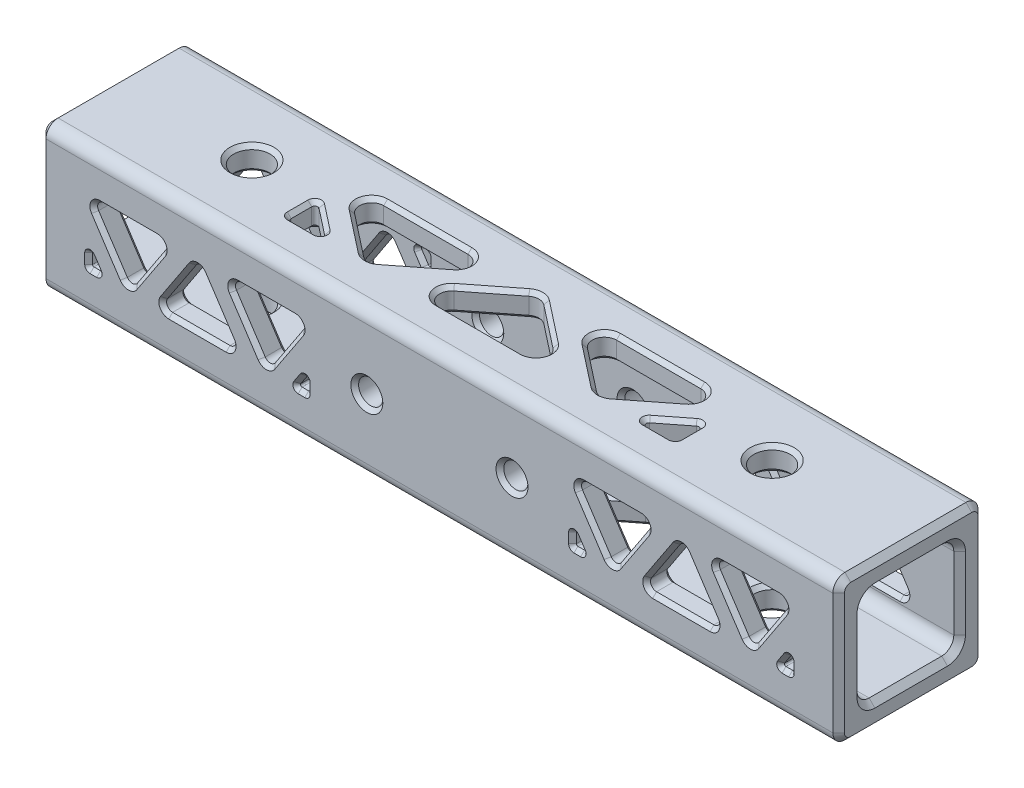
SolidWorks part; units mm, degrees
ref_plane "Front Plane" through (0, 0, 0) normal (0, 0, 1) x (1, 0, 0)
ref_plane "Top Plane" through (0, 0, 0) normal (0, 1, 0) x (1, 0, 0)
ref_plane "Right Plane" through (0, 0, 0) normal (1, 0, 0) x (0, 0, -1)
sketch "Sketch1" plane through (0, 0, 0) normal (1, 0, 0) x (0, 0, -1)
  line L1 (-6.35, -6.35) -> (6.35, -6.35)
  line L2 (-6.35, -6.35) -> (-6.35, 6.35)
  line L3 (-6.35, 6.35) -> (6.35, 6.35)
  line L4 (6.35, -6.35) -> (6.35, 6.35)
  line L5 (-6.35, -6.35) -> (6.35, 6.35) construction
  line L6 (-6.35, 6.35) -> (6.35, -6.35) construction
  line L7 (-9.525, -9.525) -> (9.525, -9.525)
  line L8 (-9.525, -9.525) -> (-9.525, 9.525)
  line L9 (-9.525, 9.525) -> (9.525, 9.525)
  line L10 (9.525, -9.525) -> (9.525, 9.525)
  line L11 (-9.525, -9.525) -> (9.525, 9.525) construction
  line L12 (-9.525, 9.525) -> (9.525, -9.525) construction
  point P0 (0, 0)
  point P6 (0, 0)
  dimension "D1" = 19.05
  dimension "D2" = 12.7
extrude "Boss-Extrude1" add sketch "Sketch1" along normal mid plane 104.775 contours L9 L10 L7 L8
hole_wizard "3/16 (0.1875) Diameter Hole1" positions "Sketch2" profile "Sketch3" hole size "3/16" standard "ANSI Inch" end condition through all
sketch "Sketch2" plane through (0, 9.525, 0) normal (0, 1, 0) x (1, 0, 0)
  line L0 (34.1313, 0) -> (-34.1313, 0) construction
  line L1 (34.1313, 0) -> (52.3875, 0) construction
  line L2 (52.3875, 9.525) -> (52.3875, -9.525) construction
  point P0 (-34.1313, 0)
  point P2 (34.1313, 0)
  dimension "D1" = 18.2562
sketch "Sketch3" plane through (-34.1313, 9.525, 0) normal (1, 0, 0) x (0, 0, 1)
  line L0 (0, 0) -> (0, 19.05)
  line L1 (0, 19.05) -> (2.3812, 19.05)
  line L2 (2.3812, 19.05) -> (2.3812, 0)
  line L5 (2.3812, 0) -> (0, 0)
  line L11 (0, -6.35) -> (0, 107.95) construction
  dimension "Thru Hole Dia." = 4.7625
  dimension "Thru Hole Depth" = 19.05
hole_wizard "1/8 (0.125) Diameter Hole1" positions "Sketch6" profile "Sketch7" hole size "1/8" standard "ANSI Inch" end condition through all
sketch "Sketch6" plane through (0, 0, -9.525) normal (0, 0, -1) x (-1, 0, 0)
  line L2 (-9.525, 0) -> (9.525, 0) construction
  point P18 (9.525, 0)
  point P20 (-9.525, 0)
  dimension "D5" = 19.05
sketch "Sketch7" plane through (9.525, 0, -9.525) normal (1, 0, 0) x (0, 1, 0)
  line L0 (0, 0) -> (0, 19.05)
  line L1 (0, 19.05) -> (1.5875, 19.05)
  line L2 (1.5875, 19.05) -> (1.5875, 0)
  line L5 (1.5875, 0) -> (0, 0)
  line L11 (0, -6.35) -> (0, 107.95) construction
  dimension "Thru Hole Dia." = 3.175
  dimension "Thru Hole Depth" = 19.05
sketch "Sketch8" plane through (0, 9.525, 0) normal (0, 1, 0) x (1, 0, 0)
  line L0 (-34.1313, 0) -> (-34.1313, 9.525) construction
  line L1 (52.3875, 9.525) -> (-52.3875, 9.525) construction
  line L2 (-34.1313, 0) -> (-34.1313, -9.525) construction
  line L3 (52.3875, -9.525) -> (-52.3875, -9.525) construction
  line L4 (-31.75, 0) -> (-31.75, -9.525) construction
  line L5 (-31.75, 0) -> (-31.75, 9.525) construction
  line L6 (34.1313, 0) -> (34.1313, 9.525) construction
  line L7 (34.1313, 0) -> (34.1313, -9.525) construction
  line L8 (31.75, 0) -> (31.75, -9.525) construction
  line L9 (31.75, 0) -> (31.75, 9.525) construction
  line L10 (-25.4, 9.525) -> (-25.4, -9.525) construction
  line L11 (25.4, 9.525) -> (25.4, -9.525) construction
  line L12 (-31.75, 0) -> (-25.4, 0) construction
  line L13 (25.4, 0) -> (31.75, 0) construction
  line L14 (-25.4, 3.9688) -> (25.4, 3.9688) construction
  line L15 (25.4, -3.9688) -> (-25.4, -3.9688) construction
  line L16 (0, -3.9688) -> (0, -9.525) construction
  line L17 (0, 3.9688) -> (0, 9.525) construction
  line L18 (-25.4, -0.0653) -> (-25.4, -3.9688)
  line L19 (-25.4, -3.9688) -> (-20.42, -3.9688)
  line L20 (-20.42, -3.9688) -> (-25.4, -0.0653)
  line L21 (-25.4, 3.9688) -> (-15.2733, -3.9688)
  line L22 (-15.2733, -3.9688) -> (-5.1467, 3.9688)
  line L23 (-5.1467, 3.9688) -> (-25.4, 3.9688)
  line L24 (-10.1267, -3.9688) -> (0, 3.9688)
  line L25 (0, 3.9688) -> (10.1267, -3.9688)
  line L26 (10.1267, -3.9688) -> (-10.1267, -3.9688)
  line L27 (25.4, 3.9688) -> (15.2733, -3.9688)
  line L28 (15.2733, -3.9688) -> (5.1467, 3.9688)
  line L29 (5.1467, 3.9688) -> (25.4, 3.9688)
  line L30 (25.4, -3.9688) -> (25.4, -0.0653)
  line L31 (25.4, -0.0653) -> (20.42, -3.9688)
  line L32 (20.42, -3.9688) -> (25.4, -3.9688)
  line L33 (-22.91, -2.017) -> (-20.9514, 0.4818) construction
  line L34 (22.91, -2.017) -> (20.9514, 0.4818) construction
  line L35 (-5.0633, 0) -> (-7.022, 2.4989) construction
  line L36 (5.0633, 0) -> (7.022, 2.4989) construction
  circle A0 centre (-34.1313, 0) radius 2.3813 construction
  circle A1 centre (34.1313, 0) radius 2.3813 construction
  dimension "D1" = 7.9375
  dimension "D2" = 6.35
  dimension "D3" = 3.175
extrude "Cut-Extrude1" cut sketch "Sketch8" against normal up to next (3.175 mm away) contours L21 L22 L23
sketch "Sketch9" plane through (0, 0, 9.525) normal (0, 0, 1) x (1, 0, 0)
  line L0 (-9.525, 0) -> (-9.525, -9.525) construction
  line L1 (52.3875, -9.525) -> (-52.3875, -9.525) construction
  line L2 (-9.525, 0) -> (-9.525, 9.525) construction
  line L3 (52.3875, 9.525) -> (-52.3875, 9.525) construction
  line L4 (-11.1125, 0) -> (-11.1125, -9.525) construction
  line L5 (-11.1125, 0) -> (-11.1125, 9.525) construction
  line L6 (-46.0375, 3.9688) -> (-46.0375, -3.9687) construction
  line L7 (-46.0375, -3.9687) -> (-17.4625, -3.9688) construction
  line L8 (-11.1125, 0) -> (-17.4625, 0) construction
  line L9 (-46.0375, 0) -> (-52.3875, 0) construction
  line L10 (-52.3875, 9.525) -> (-52.3875, -9.525) construction
  line L11 (-46.0375, 3.9688) -> (-17.4625, 3.9688) construction
  line L12 (-17.4625, -3.9688) -> (-17.4625, 3.9688) construction
  line L13 (-31.75, -3.9687) -> (-31.75, -9.525) construction
  line L14 (-31.75, 3.9687) -> (-31.75, 9.525) construction
  line L15 (9.525, 0) -> (9.525, -9.525) construction
  line L16 (9.525, 0) -> (9.525, 9.525) construction
  line L17 (11.1125, 0) -> (11.1125, -9.525) construction
  line L18 (11.1125, 0) -> (11.1125, 9.525) construction
  line L19 (17.4625, 3.9688) -> (17.4625, -3.9688) construction
  line L20 (17.4625, -3.9688) -> (46.0375, -3.9688) construction
  line L21 (46.0375, -3.9688) -> (46.0375, 3.9688) construction
  line L22 (46.0375, 3.9688) -> (17.4625, 3.9688) construction
  line L23 (11.1125, 0) -> (17.4625, 0) construction
  line L24 (46.0375, 0) -> (52.3875, 0) construction
  line L25 (52.3875, 9.525) -> (52.3875, -9.525) construction
  line L26 (31.75, -3.9688) -> (31.75, -9.525) construction
  line L27 (31.75, 3.9688) -> (31.75, 9.525) construction
  line L28 (-7.9375, 0) -> (-7.9375, -9.525) construction
  line L29 (-7.9375, 0) -> (-7.9375, 9.525) construction
  line L30 (7.9375, 0) -> (7.9375, -9.525) construction
  line L31 (7.9375, 0) -> (7.9375, 9.525) construction
  line L32 (-1.5875, 3.9687) -> (1.5875, 3.9687) construction
  line L33 (1.5875, 3.9687) -> (1.5875, -3.9687) construction
  line L34 (1.5875, -3.9687) -> (-1.5875, -3.9687) construction
  line L35 (-1.5875, -3.9687) -> (-1.5875, 3.9687) construction
  line L36 (-7.9375, 0) -> (-1.5875, 0) construction
  line L37 (1.5875, 0) -> (7.9375, 0) construction
  line L38 (-46.0375, 3.9688) -> (-40.7961, -3.9688)
  line L39 (-40.7961, -3.9688) -> (-35.5548, 3.9688)
  line L40 (-35.5548, 3.9688) -> (-46.0375, 3.9688)
  line L41 (-36.9914, -3.9688) -> (-31.75, 3.9687)
  line L42 (-31.75, 3.9687) -> (-26.5086, -3.9688)
  line L43 (-26.5086, -3.9688) -> (-36.9914, -3.9688)
  line L44 (-17.4625, 3.9688) -> (-22.7039, -3.9688)
  line L45 (-22.7039, -3.9688) -> (-27.9452, 3.9688)
  line L46 (-27.9452, 3.9688) -> (-17.4625, 3.9688)
  line L47 (-22.7039, -3.9688) -> (-22.7039, 3.9688) construction
  line L48 (-31.75, 3.9687) -> (-31.75, -3.9687) construction
  line L49 (-40.7961, -3.9688) -> (-40.7961, 3.9688) construction
  line L50 (-46.0375, -1.7931) -> (-46.0375, -3.9687)
  line L51 (-46.0375, -3.9687) -> (-44.6009, -3.9688)
  line L52 (-44.6009, -3.9688) -> (-46.0375, -1.7931)
  line L53 (-17.4625, -3.9688) -> (-17.4625, -1.7931)
  line L54 (-17.4625, -1.7931) -> (-18.8991, -3.9688)
  line L55 (-18.8991, -3.9688) -> (-17.4625, -3.9688)
  line L56 (-18.1808, -2.8809) -> (-20.8303, -1.1314) construction
  line L57 (-45.3192, -2.8809) -> (-42.6697, -1.1314) construction
  line L58 (-34.3707, 0) -> (-37.0202, 1.7495) construction
  line L59 (-29.1293, 0) -> (-26.4798, 1.7495) construction
  line L60 (17.4625, 3.9688) -> (22.7039, -3.9688)
  line L61 (22.7039, -3.9688) -> (27.9452, 3.9688)
  line L62 (27.9452, 3.9688) -> (17.4625, 3.9688)
  line L63 (26.5086, -3.9688) -> (31.75, 3.9688)
  line L64 (31.75, 3.9688) -> (36.9914, -3.9688)
  line L65 (36.9914, -3.9688) -> (26.5086, -3.9688)
  line L66 (46.0375, 3.9688) -> (40.7961, -3.9688)
  line L67 (40.7961, -3.9688) -> (35.5548, 3.9688)
  line L68 (35.5548, 3.9688) -> (46.0375, 3.9688)
  line L69 (17.4625, -1.7931) -> (17.4625, -3.9688)
  line L70 (17.4625, -3.9688) -> (18.8991, -3.9688)
  line L71 (18.8991, -3.9688) -> (17.4625, -1.7931)
  line L72 (46.0375, -1.7931) -> (46.0375, -3.9688)
  line L73 (46.0375, -3.9688) -> (44.6009, -3.9688)
  line L74 (44.6009, -3.9688) -> (46.0375, -1.7931)
  line L75 (18.1808, -2.8809) -> (20.8303, -1.1314) construction
  line L76 (29.1293, 0) -> (26.4798, 1.7495) construction
  line L77 (34.3707, 0) -> (37.0202, 1.7495) construction
  line L78 (45.3192, -2.8809) -> (42.6697, -1.1314) construction
  circle A0 centre (-9.525, 0) radius 1.5875 construction
  circle A1 centre (9.525, 0) radius 1.5875 construction
  dimension "D1" = 6.35
  dimension "D2" = 7.9375
  dimension "D3" = 7.9375
  dimension "D4" = 6.35
  dimension "D5" = 3.175
extrude "Cut-Extrude2" cut sketch "Sketch9" against normal up to next (3.175 mm away)
ref_axis "Axis1" through (57.6262, 0, 0) along (-1, 0, 0)
pattern_circular "CirPattern1" count 2 over 360 about axis through (57.6262, 0, 0) along (-1, 0, 0) of "Cut-Extrude1"
pattern_circular "CirPattern2" count 2 over 360 about axis through (57.6262, 0, 0) along (-1, 0, 0) of "Cut-Extrude2"
fillet "Fillet1" radius 1.5875 26 edges at (0, -6.35, -6.35) (0, 6.35, -6.35) (0, 6.35, 6.35) (0, -6.35, 6.35) (0, -9.525, -9.525) (0, 9.525, -9.525) (0, -9.525, 9.525) (0, 9.525, 9.525) (25.4, -7.9375, 3.9688) (5.1467, -7.9375, 3.9688) (15.2733, -7.9375, -3.9687) (0, -7.9375, 3.9688) (10.1267, -7.9375, -3.9688) (-10.1267, -7.9375, -3.9688) (-5.1467, -7.9375, 3.9688) (-25.4, -7.9375, 3.9688) (-15.2733, -7.9375, -3.9688) (25.4, 7.9375, -3.9688) (5.1467, 7.9375, -3.9687) (15.2733, 7.9375, 3.9688) (10.1267, 7.9375, 3.9688) (0, 7.9375, -3.9688) (-10.1267, 7.9375, 3.9687) (-5.1467, 7.9375, -3.9688) (-25.4, 7.9375, -3.9687) (-15.2733, 7.9375, 3.9688)
fillet "Fillet4" radius 0.7937 36 edges at (46.0375, 3.9688, 7.9375) (40.7961, -3.9688, 7.9375) (35.5548, 3.9688, 7.9375) (31.75, 3.9688, 7.9375) (36.9914, -3.9688, 7.9375) (26.5086, -3.9688, 7.9375) (17.4625, 3.9688, 7.9375) (27.9452, 3.9688, 7.9375) (22.7039, -3.9688, 7.9375) (-17.4625, 3.9688, 7.9375) (-22.7039, -3.9688, 7.9375) (-27.9452, 3.9688, 7.9375) (-26.5086, -3.9688, 7.9375) (-36.9914, -3.9688, 7.9375) (-31.75, 3.9687, 7.9375) (-35.5548, 3.9688, 7.9375) (-40.7961, -3.9688, 7.9375) (-46.0375, 3.9688, 7.9375) (-40.7961, 3.9688, -7.9375) (-46.0375, -3.9688, -7.9375) (-35.5548, -3.9688, -7.9375) (-36.9914, 3.9688, -7.9375) (-26.5086, 3.9688, -7.9375) (-31.75, -3.9687, -7.9375) (-27.9452, -3.9688, -7.9375) (-17.4625, -3.9688, -7.9375) (-22.7039, 3.9688, -7.9375) (17.4625, -3.9688, -7.9375) (27.9452, -3.9688, -7.9375) (22.7039, 3.9688, -7.9375) (26.5086, 3.9687, -7.9375) (36.9914, 3.9688, -7.9375) (31.75, -3.9688, -7.9375) (35.5548, -3.9688, -7.9375) (40.7961, 3.9688, -7.9375) (46.0375, -3.9688, -7.9375)
fillet "Fillet2" radius 0.3969 12 edges at (20.42, 7.9375, 3.9688) (25.4, 7.9375, 0.0653) (25.4, 7.9375, 3.9688) (-25.4, 7.9375, 0.0653) (-20.42, 7.9375, 3.9688) (-25.4, 7.9375, 3.9688) (-25.4, -7.9375, -0.0653) (-20.42, -7.9375, -3.9688) (-25.4, -7.9375, -3.9688) (20.42, -7.9375, -3.9688) (25.4, -7.9375, -0.0653) (25.4, -7.9375, -3.9688)
fillet "Fillet3" radius 0.1984 24 edges at (-46.0375, 3.9687, -7.9375) (-46.0375, 1.7931, -7.9375) (-44.6009, 3.9688, -7.9375) (-18.8991, 3.9688, -7.9375) (-17.4625, 1.7931, -7.9375) (-17.4625, 3.9688, -7.9375) (17.4625, 3.9688, -7.9375) (17.4625, 1.7931, -7.9375) (18.8991, 3.9688, -7.9375) (44.6009, 3.9688, -7.9375) (46.0375, 3.9688, -7.9375) (46.0375, 1.7931, -7.9375) (46.0375, -3.9688, 7.9375) (46.0375, -1.7931, 7.9375) (44.6009, -3.9688, 7.9375) (18.8991, -3.9688, 7.9375) (17.4625, -1.7931, 7.9375) (17.4625, -3.9688, 7.9375) (-18.8991, -3.9688, 7.9375) (-17.4625, -1.7931, 7.9375) (-17.4625, -3.9688, 7.9375) (-44.6009, -3.9688, 7.9375) (-46.0375, -1.7931, 7.9375) (-46.0375, -3.9687, 7.9375)
chamfer "Chamfer1" distance 0.762 angle 45 32 edges at (-52.3875, 5.885, 5.885) (-52.3875, 6.35, 0) (-52.3875, 5.885, -5.885) (-52.3875, 0, -6.35) (-52.3875, -5.885, -5.885) (-52.3875, -6.35, 0) (-52.3875, -5.885, 5.885) (-52.3875, 0, 6.35) (-52.3875, 9.06, -9.06) (-52.3875, 9.525, 0) (-52.3875, 9.06, 9.06) (-52.3875, 0, 9.525) (-52.3875, -9.06, 9.06) (-52.3875, -9.525, 0) (-52.3875, -9.06, -9.06) (-52.3875, 0, -9.525) (52.3875, 5.885, -5.885) (52.3875, 6.35, 0) (52.3875, 5.885, 5.885) (52.3875, 0, 6.35) (52.3875, -5.885, 5.885) (52.3875, -6.35, 0) (52.3875, -5.885, -5.885) (52.3875, 0, -6.35) (52.3875, -9.06, 9.06) (52.3875, 0, 9.525) (52.3875, 9.06, 9.06) (52.3875, 9.525, 0) (52.3875, 9.06, -9.06) (52.3875, 0, -9.525) (52.3875, -9.06, -9.06) (52.3875, -9.525, 0)
chamfer "Chamfer2" distance 0.508 angle 45 376 edges at (34.1313, 6.35, -2.3812) (34.1313, -6.35, 2.3812) (34.1313, -9.525, 2.3812) (34.1313, 9.525, 2.3813) (15.2733, -9.525, 3.9688) (15.2733, -6.35, 3.9688) (19.0167, -9.525, -1.0347) (19.0167, -6.35, -1.0347) (11.53, -9.525, -1.0347) (11.53, -6.35, -1.0347) (-3.7433, -9.525, 1.0347) (-3.7433, -6.35, 1.0347) (3.7433, -9.525, 1.0347) (3.7433, -6.35, 1.0347) (0, -9.525, -3.9688) (0, -6.35, -3.9688) (-15.2733, -9.525, 3.9688) (-15.2733, -6.35, 3.9688) (-34.1313, 6.35, -2.3812) (-34.1313, -6.35, 2.3812) (-11.53, -9.525, -1.0347) (-11.53, -6.35, -1.0347) (-34.1313, -9.525, 2.3812) (-34.1313, 9.525, 2.3813) (-19.0167, -9.525, -1.0347) (-19.0167, -6.35, -1.0347) (15.2733, 9.525, -3.9688) (15.2733, 6.35, -3.9688) (19.0167, 9.525, 1.0347) (19.0167, 6.35, 1.0347) (11.53, 9.525, 1.0347) (11.53, 6.35, 1.0347) (3.7433, 9.525, -1.0347) (3.7433, 6.35, -1.0347) (0, 9.525, 3.9688) (0, 6.35, 3.9688) (-3.7433, 9.525, -1.0347) (-3.7433, 6.35, -1.0347) (-15.2733, 9.525, -3.9688) (-15.2733, 6.35, -3.9688) (-11.53, 9.525, 1.0347) (-11.53, 6.35, 1.0347) (-19.0167, 9.525, 1.0347) (-19.0167, 6.35, 1.0347) (22.3019, -9.525, 2.8993) (22.3019, -6.35, 2.8993) (8.2448, -9.525, 2.8993) (8.2448, -6.35, 2.8993) (15.2733, -9.525, -3.5392) (15.2733, -6.35, -3.5392) (0, -9.525, 3.5392) (0, -6.35, 3.5392) (7.0286, -9.525, -2.8993) (7.0286, -6.35, -2.8993) (-7.0286, -9.525, -2.8993) (-7.0286, -6.35, -2.8993) (-8.2448, -9.525, 2.8993) (-8.2448, -6.35, 2.8993) (-22.3019, -9.525, 2.8993) (-22.3019, -6.35, 2.8993) (-15.2733, -9.525, -3.5392) (-15.2733, -6.35, -3.5392) (22.3019, 9.525, -2.8993) (22.3019, 6.35, -2.8993) (8.2448, 9.525, -2.8993) (8.2448, 6.35, -2.8993) (15.2733, 9.525, 3.5392) (15.2733, 6.35, 3.5392) (7.0286, 9.525, 2.8993) (7.0286, 6.35, 2.8993) (0, 9.525, -3.5392) (0, 6.35, -3.5392) (-7.0286, 9.525, 2.8993) (-7.0286, 6.35, 2.8993) (-8.2448, 9.525, -2.8993) (-8.2448, 6.35, -2.8993) (-22.3019, 9.525, -2.8993) (-22.3019, 6.35, -2.8993) (-15.2733, 9.525, 3.5392) (-15.2733, 6.35, 3.5392) (7.9375, 0, 6.35) (11.1125, 0, -6.35) (7.9375, 0, -9.525) (7.9375, 0, 9.525) (-38.2507, 0.114, -9.525) (-38.2507, 0.114, -6.35) (-43.3415, 0.114, -9.525) (-43.3415, 0.114, -6.35) (-40.7961, -3.9688, -9.525) (-40.7961, -3.9688, -6.35) (-31.75, 3.9688, -9.525) (-31.75, 3.9688, -6.35) (-34.2954, -0.114, -9.525) (-34.2954, -0.114, -6.35) (-29.2046, -0.114, -9.525) (-29.2046, -0.114, -6.35) (-25.2493, 0.114, -9.525) (-25.2493, 0.114, -6.35) (-22.7039, -3.9688, -9.525) (-22.7039, -3.9688, -6.35) (-20.1585, 0.114, -9.525) (-20.1585, 0.114, -6.35) (20.1585, 0.114, -9.525) (20.1585, 0.114, -6.35) (22.7039, -3.9688, -9.525) (22.7039, -3.9688, -6.35) (25.2493, 0.114, -9.525) (25.2493, 0.114, -6.35) (31.75, 3.9688, -9.525) (-7.9375, 0, -6.35) (31.75, 3.9688, -6.35) (-11.1125, 0, 6.35) (29.2046, -0.114, -9.525) (-11.1125, 0, 9.525) (29.2046, -0.114, -6.35) (-11.1125, 0, -9.525) (34.2954, -0.114, -9.525) (34.2954, -0.114, -6.35) (38.2507, 0.114, -9.525) (38.2507, 0.114, -6.35) (40.7961, -3.9688, -9.525) (40.7961, -3.9688, -6.35) (43.3415, 0.114, -9.525) (43.3415, 0.114, -6.35) (40.7961, 3.9688, 9.525) (40.7961, 3.9688, 6.35) (43.3415, -0.114, 9.525) (43.3415, -0.114, 6.35) (38.2507, -0.114, 9.525) (38.2507, -0.114, 6.35) (29.2046, 0.114, 9.525) (29.2046, 0.114, 6.35) (34.2954, 0.114, 9.525) (34.2954, 0.114, 6.35) (31.75, -3.9688, 9.525) (31.75, -3.9688, 6.35) (20.1585, -0.114, 9.525) (20.1585, -0.114, 6.35) (22.7039, 3.9688, 9.525) (22.7039, 3.9688, 6.35) (25.2493, -0.114, 9.525) (25.2493, -0.114, 6.35) (-22.7039, 3.9688, 9.525) (-22.7039, 3.9688, 6.35) (-20.1585, -0.114, 9.525) (-20.1585, -0.114, 6.35) (-25.2493, -0.114, 9.525) (-25.2493, -0.114, 6.35) (-29.2046, 0.114, 9.525) (-29.2046, 0.114, 6.35) (-31.75, -3.9688, 9.525) (-31.75, -3.9688, 6.35) (-34.2954, 0.114, 9.525) (-34.2954, 0.114, 6.35) (-40.7961, 3.9688, 9.525) (-40.7961, 3.9688, 6.35) (-38.2507, -0.114, 9.525) (-38.2507, -0.114, 6.35) (-43.3415, -0.114, 9.525) (-43.3415, -0.114, 6.35) (-40.7961, 3.322, -9.525) (-40.7961, 3.322, -6.35) (-45.2612, -3.5511, -9.525) (-45.2612, -3.5511, -6.35) (-36.3311, -3.5511, -9.525) (-36.3311, -3.5511, -6.35) (-36.2151, 3.5511, -9.525) (-36.2151, 3.5511, -6.35) (-27.2849, 3.5511, -9.525) (-27.2849, 3.5511, -6.35) (-31.75, -3.322, -9.525) (-31.75, -3.322, -6.35) (-27.1689, -3.5511, -9.525) (-27.1689, -3.5511, -6.35) (-18.2388, -3.5511, -9.525) (-18.2388, -3.5511, -6.35) (-22.7039, 3.322, -9.525) (-22.7039, 3.322, -6.35) (18.2388, -3.5511, -9.525) (18.2388, -3.5511, -6.35) (27.1689, -3.5511, -9.525) (27.1689, -3.5511, -6.35) (22.7039, 3.322, -9.525) (22.7039, 3.322, -6.35) (27.2849, 3.5511, -9.525) (27.2849, 3.5511, -6.35) (36.2151, 3.5511, -9.525) (36.2151, 3.5511, -6.35) (31.75, -3.322, -9.525) (31.75, -3.322, -6.35) (36.3311, -3.5511, -9.525) (36.3311, -3.5511, -6.35) (40.7961, 3.322, -9.525) (40.7961, 3.322, -6.35) (45.2612, -3.5511, -9.525) (45.2612, -3.5511, -6.35) (45.2612, 3.5511, 9.525) (45.2612, 3.5511, 6.35) (40.7961, -3.322, 9.525) (40.7961, -3.322, 6.35) (36.3311, 3.5511, 9.525) (36.3311, 3.5511, 6.35) (31.75, 3.322, 9.525) (31.75, 3.322, 6.35) (36.2151, -3.5511, 9.525) (36.2151, -3.5511, 6.35) (27.2849, -3.5511, 9.525) (27.2849, -3.5511, 6.35) (18.2388, 3.5511, 9.525) (18.2388, 3.5511, 6.35) (27.1689, 3.5511, 9.525) (27.1689, 3.5511, 6.35) (22.7039, -3.322, 9.525) (22.7039, -3.322, 6.35) (-18.2388, 3.5511, 9.525) (-18.2388, 3.5511, 6.35) (-22.7039, -3.322, 9.525) (-22.7039, -3.322, 6.35) (-27.1689, 3.5511, 9.525) (-27.1689, 3.5511, 6.35) (-27.2849, -3.5511, 9.525) (-27.2849, -3.5511, 6.35) (-36.2151, -3.5511, 9.525) (-36.2151, -3.5511, 6.35) (-31.75, 3.322, 9.525) (-31.75, 3.322, 6.35) (-36.3311, 3.5511, 9.525) (-36.3311, 3.5511, 6.35) (-40.7961, -3.322, 9.525) (-40.7961, -3.322, 6.35) (-45.2612, 3.5511, 9.525) (-45.2612, 3.5511, 6.35) (23.2864, 9.525, 3.9688) (23.2864, 6.35, 3.9688) (23.0416, 9.525, 1.9139) (23.0416, 6.35, 1.9139) (25.4, 9.525, 2.2263) (25.4, 6.35, 2.2263) (-25.4, 9.525, 2.2263) (-25.4, 6.35, 2.2263) (-23.0416, 9.525, 1.9139) (-23.0416, 6.35, 1.9139) (-23.2864, 9.525, 3.9688) (-23.2864, 6.35, 3.9688) (-25.4, -9.525, -2.2263) (-25.4, -6.35, -2.2263) (-23.0416, -9.525, -1.9139) (-23.0416, -6.35, -1.9139) (-23.2864, -9.525, -3.9688) (-23.2864, -6.35, -3.9688) (23.2864, -9.525, -3.9688) (23.2864, -6.35, -3.9688) (23.0416, -9.525, -1.9139) (23.0416, -6.35, -1.9139) (25.4, -9.525, -2.2263) (25.4, -6.35, -2.2263) (21.1946, 9.525, 3.7014) (21.1946, 6.35, 3.7014) (25.1768, 9.525, 0.5238) (25.1768, 6.35, 0.5238) (25.2838, 9.525, 3.8525) (25.2838, 6.35, 3.8525) (-25.1768, 9.525, 0.5238) (-25.1768, 6.35, 0.5238) (-21.1946, 9.525, 3.7014) (-21.1946, 6.35, 3.7014) (-25.2838, 9.525, 3.8525) (-25.2838, 6.35, 3.8525) (-25.1768, -9.525, -0.5238) (-25.1768, -6.35, -0.5238) (-21.1946, -9.525, -3.7014) (-21.1946, -6.35, -3.7014) (-25.2838, -9.525, -3.8525) (-25.2838, -6.35, -3.8525) (21.1946, -9.525, -3.7014) (21.1946, -6.35, -3.7014) (25.1768, -9.525, -0.5238) (25.1768, -6.35, -0.5238) (25.2838, -9.525, -3.8525) (25.2838, -6.35, -3.8525) (-45.4044, 3.9687, -9.525) (-45.4044, 3.9687, -6.35) (-46.0375, 3.112, -9.525) (-46.0375, 3.112, -6.35) (-45.2388, 3.0027, -9.525) (-45.2388, 3.0027, -6.35) (-18.0956, 3.9688, -9.525) (-18.0956, 3.9688, -6.35) (-18.2612, 3.0027, -9.525) (-18.2612, 3.0027, -6.35) (-17.4625, 3.112, -9.525) (-17.4625, 3.112, -6.35) (18.0956, 3.9688, -9.525) (18.0956, 3.9688, -6.35) (17.4625, 3.112, -9.525) (17.4625, 3.112, -6.35) (18.2612, 3.0027, -9.525) (18.2612, 3.0027, -6.35) (45.4044, 3.9688, -9.525) (45.4044, 3.9688, -6.35) (45.2388, 3.0027, -9.525) (45.2388, 3.0027, -6.35) (46.0375, 3.112, -9.525) (46.0375, 3.112, -6.35) (46.0375, -3.112, 9.525) (46.0375, -3.112, 6.35) (45.4044, -3.9688, 9.525) (45.4044, -3.9688, 6.35) (45.2388, -3.0027, 9.525) (45.2388, -3.0027, 6.35) (18.2612, -3.0027, 9.525) (18.2612, -3.0027, 6.35) (18.0956, -3.9688, 9.525) (18.0956, -3.9688, 6.35) (17.4625, -3.112, 9.525) (17.4625, -3.112, 6.35) (-18.0956, -3.9688, 9.525) (-18.0956, -3.9688, 6.35) (-18.2612, -3.0027, 9.525) (-18.2612, -3.0027, 6.35) (-17.4625, -3.112, 9.525) (-17.4625, -3.112, 6.35) (-45.2388, -3.0027, 9.525) (-45.2388, -3.0027, 6.35) (-45.4044, -3.9687, 9.525) (-45.4044, -3.9687, 6.35) (-46.0375, -3.112, 9.525) (-46.0375, -3.112, 6.35) (-45.9794, 3.9106, -9.525) (-45.9794, 3.9106, -6.35) (-45.8961, 2.2637, -9.525) (-45.8961, 2.2637, -6.35) (-44.795, 3.8643, -9.525) (-44.795, 3.8643, -6.35) (-18.705, 3.8643, -9.525) (-18.705, 3.8643, -6.35) (-17.6039, 2.2637, -9.525) (-17.6039, 2.2637, -6.35) (-17.5206, 3.9106, -9.525) (-17.5206, 3.9106, -6.35) (17.5206, 3.9106, -9.525) (17.5206, 3.9106, -6.35) (17.6039, 2.2637, -9.525) (17.6039, 2.2637, -6.35) (18.705, 3.8643, -9.525) (18.705, 3.8643, -6.35) (44.795, 3.8643, -9.525) (44.795, 3.8643, -6.35) (45.9794, 3.9106, -9.525) (45.9794, 3.9106, -6.35) (45.8961, 2.2637, -9.525) (45.8961, 2.2637, -6.35) (45.9794, -3.9106, 9.525) (45.9794, -3.9106, 6.35) (45.8961, -2.2637, 9.525) (45.8961, -2.2637, 6.35) (44.795, -3.8643, 9.525) (44.795, -3.8643, 6.35) (18.705, -3.8643, 9.525) (18.705, -3.8643, 6.35) (17.6039, -2.2637, 9.525) (17.6039, -2.2637, 6.35) (17.5206, -3.9106, 9.525) (17.5206, -3.9106, 6.35) (-18.705, -3.8643, 9.525) (-18.705, -3.8643, 6.35) (-17.6039, -2.2637, 9.525) (-17.6039, -2.2637, 6.35) (-17.5206, -3.9106, 9.525) (-17.5206, -3.9106, 6.35) (-44.795, -3.8643, 9.525) (-44.795, -3.8643, 6.35) (-45.8961, -2.2637, 9.525) (-45.8961, -2.2637, 6.35) (-45.9794, -3.9106, 9.525) (-45.9794, -3.9106, 6.35)
